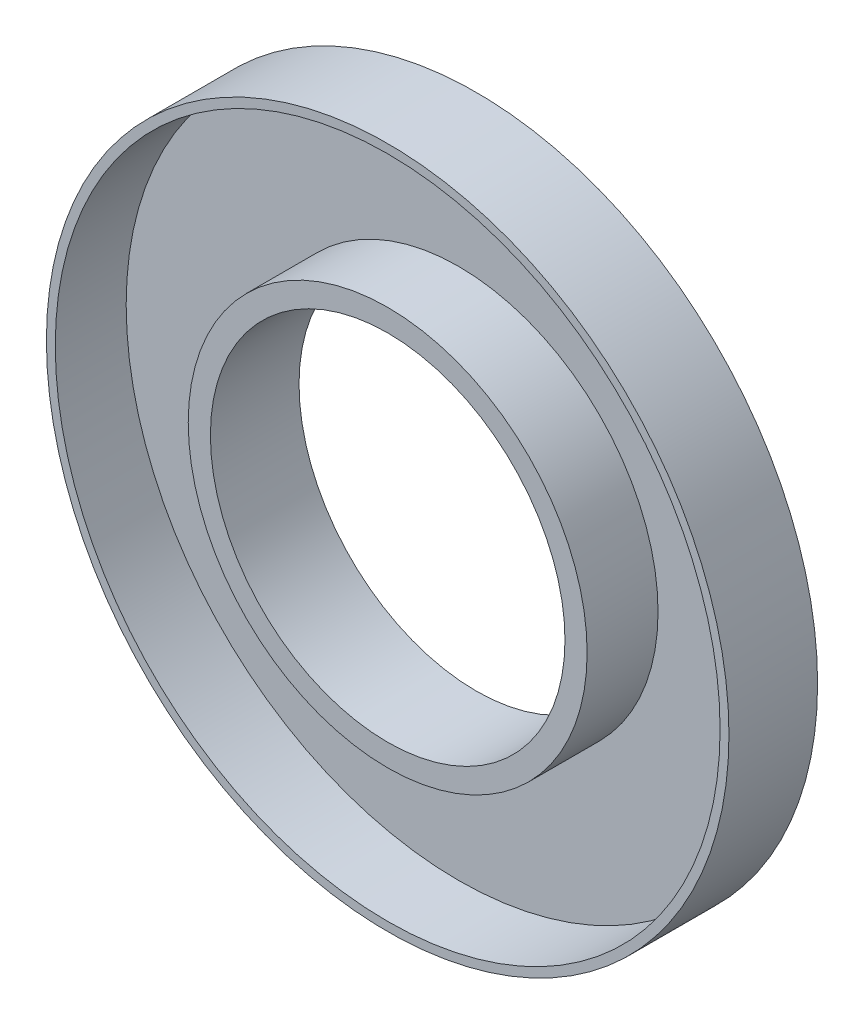
SolidWorks part; units mm, degrees
ref_plane "Front Plane" through (0, 0, 0) normal (0, 0, 1) x (1, 0, 0)
ref_plane "Top Plane" through (0, 0, 0) normal (0, 1, 0) x (1, 0, 0)
ref_plane "Right Plane" through (0, 0, 0) normal (1, 0, 0) x (0, 0, -1)
sketch "Sketch1" plane through (0, 0, 0) normal (0, 0, 1) x (1, 0, 0)
  circle A0 centre (0, 0) radius 19.25
  dimension "D2" = 38.5
extrude "Boss-Extrude1" add sketch "Sketch1" along normal blind 1
sketch "Sketch2" plane through (0, 0, 1) normal (0, 0, 1) x (1, 0, 0)
  circle A0 centre (0, 0) radius 10
  circle A1 centre (0, 0) radius 11.25
  dimension "D1" = 22.5
  dimension "D2" = 20
extrude "Boss-Extrude2" add sketch "Sketch2" along normal blind 4
sketch "Sketch3" plane through (0, 0, 1) normal (0, 0, 1) x (1, 0, 0)
  circle A0 centre (0, 0) radius 18.75
  circle A1 centre (0, 0) radius 19.25
  circle A2 centre (0, 0) radius 19.25 construction
  dimension "D1" = 37.5
extrude "Boss-Extrude3" add sketch "Sketch3" along normal up to surface (4 mm away) up to face at (11.25, 0, 5)
sketch "Sketch5" plane through (0, 0, 1) normal (0, 0, 1) x (1, 0, 0)
  circle A0 centre (0, 0) radius 10
extrude "Cut-Extrude1" cut sketch "Sketch5" against normal blind 5
